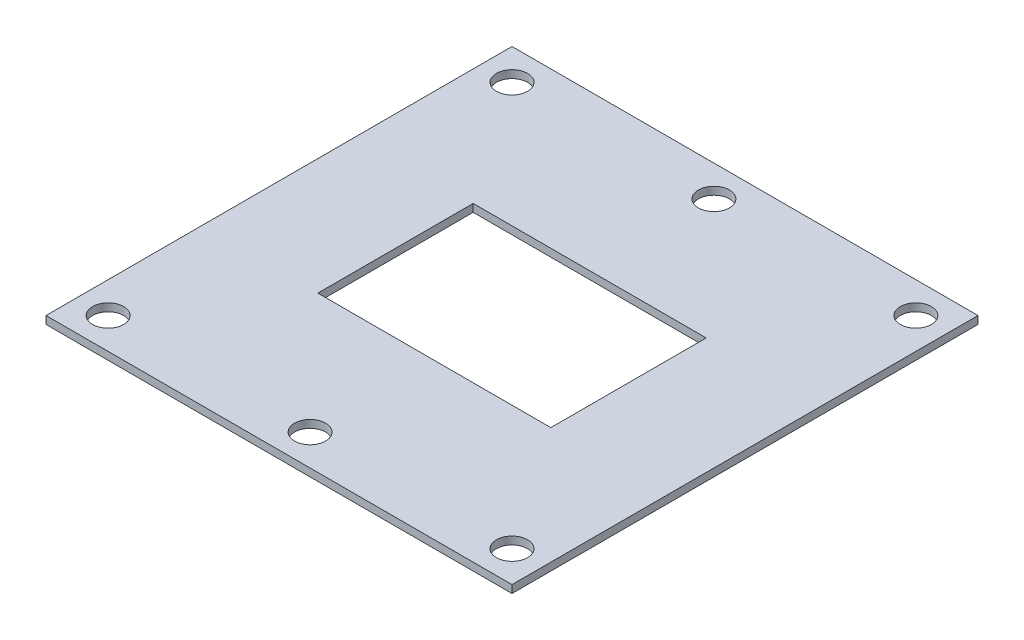
SolidWorks part; units mm, degrees
ref_plane "Front Plane" through (0, 0, 0) normal (0, 0, 1) x (1, 0, 0)
ref_plane "Top Plane" through (0, 0, 0) normal (0, 1, 0) x (1, 0, 0)
ref_plane "Right Plane" through (0, 0, 0) normal (1, 0, 0) x (0, 0, -1)
sketch "Sketch1" plane through (0, 0, 0) normal (0, 1, 0) x (1, 0, 0)
  line L1 (30, -30) -> (-30, -30)
  line L2 (30, -30) -> (30, 30)
  line L3 (30, 30) -> (-30, 30)
  line L4 (-30, -30) -> (-30, 30)
  line L5 (30, -30) -> (-30, 30) construction
  line L6 (30, 30) -> (-30, -30) construction
  point P0 (0, 0)
  dimension "D1" = 60
  dimension "D2" = 60
extrude "Boss-Extrude1" add sketch "Sketch1" along normal blind 1
hole_wizard "Ø4.0 (4) Diameter Hole1" positions "Sketch13" profile "Sketch12" hole size "Ø4.0" standard "ANSI Metric" end condition up to next
sketch "Sketch13" plane through (0, 1, 0) normal (0, 1, 0) x (1, 0, 0)
  line L0 (0, 30) -> (0, -30) construction
  line L1 (30, 30) -> (-30, 30) construction
  line L2 (-30, -30) -> (30, -30) construction
  line L4 (-30, 0) -> (30, 0) construction
  line L5 (-30, 30) -> (-30, -30) construction
  line L6 (30, -30) -> (30, 30) construction
  point P17 (26, 26)
  point P24 (0, 26)
  point P27 (-26, 26)
  point P28 (0, -26)
  point P29 (26, -26)
  point P30 (-26, -26)
  dimension "D1" = 4
  dimension "D2" = 4
sketch "Sketch12" plane through (26, 1, -26) normal (1, 0, 0) x (0, 0, 1)
  line L0 (0, 0) -> (0, 1)
  line L1 (0, 1) -> (2, 1)
  line L2 (2, 1) -> (2, 0)
  line L5 (2, 0) -> (0, 0)
  line L11 (0, -6.35) -> (0, 107.95) construction
  dimension "Thru Hole Dia." = 4
  dimension "Thru Hole Depth" = 1
sketch "Sketch14" plane through (0, 1, 0) normal (0, 1, 0) x (1, 0, 0)
  line L3 (15, -10) -> (-15, -10)
  line L6 (15, -10) -> (15, 10)
  line L7 (15, 10) -> (-15, 10)
  line L8 (-15, -10) -> (-15, 10)
  line L9 (15, -10) -> (-15, 10) construction
  line L10 (15, 10) -> (-15, -10) construction
  point P0 (0, 0)
  dimension "D1" = 30
  dimension "D2" = 20
extrude "Cut-Extrude1" cut sketch "Sketch14" against normal blind 10
